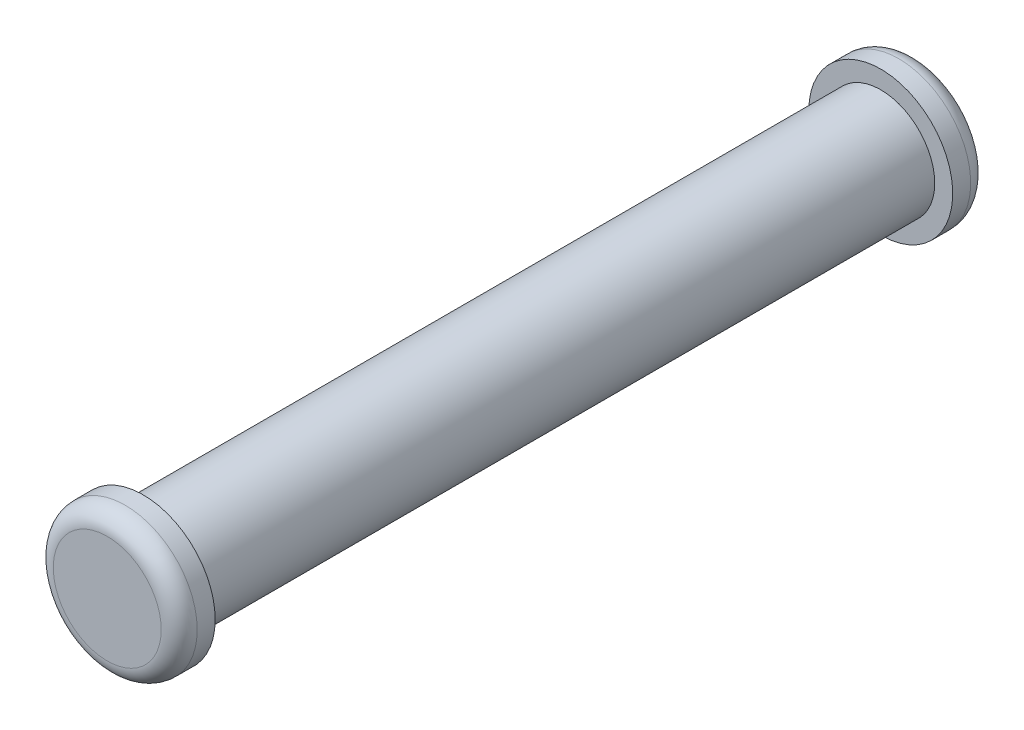
SolidWorks part; units mm, degrees
ref_plane "Front Plane" through (0, 0, 0) normal (0, 0, 1) x (1, 0, 0)
ref_plane "Top Plane" through (0, 0, 0) normal (0, 1, 0) x (1, 0, 0)
ref_plane "Right Plane" through (0, 0, 0) normal (1, 0, 0) x (0, 0, -1)
sketch "Sketch1" plane through (0, 0, 0) normal (0, 0, 1) x (1, 0, 0)
  circle A0 centre (0, 0) radius 1.5
  dimension "D1" = 3
extrude "Boss-Extrude1" add sketch "Sketch1" along normal blind 20.5
sketch "Sketch2" plane through (0, 0, 0) normal (0, 0, -1) x (-1, 0, 0)
  circle A0 centre (0, 0) radius 2
  dimension "D1" = 4
extrude "Boss-Extrude2" add sketch "Sketch2" along normal blind 1
sketch "Sketch3" plane through (0, 0, 20.5) normal (0, 0, 1) x (1, 0, 0)
  circle A1 centre (0, 0) radius 2
  circle A2 centre (0, 0) radius 2
  dimension "D1" = 0
extrude "Boss-Extrude3" add sketch "Sketch3" along normal blind 1
fillet "Fillet1" radius 0.5 2 edges at (-2, 0, -1) (2, 0, 21.5)
